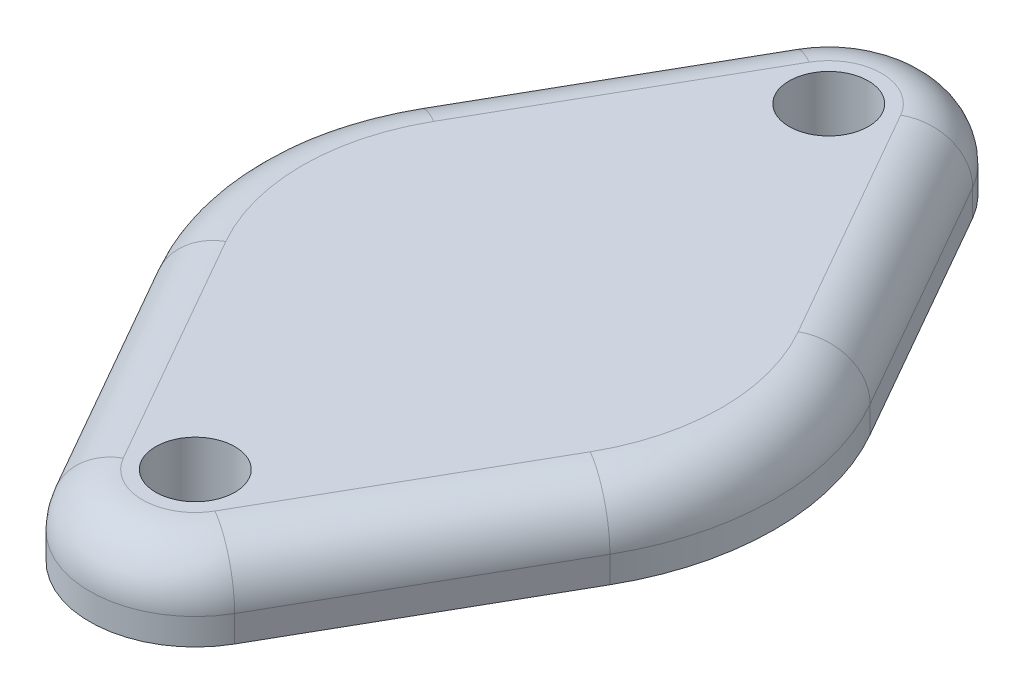
SolidWorks part; units mm, degrees
ref_plane "Спереди" through (0, 0, 0) normal (0, 0, 1) x (1, 0, 0)
ref_plane "Сверху" through (0, 0, 0) normal (0, 1, 0) x (1, 0, 0)
ref_plane "Справа" through (0, 0, 0) normal (1, 0, 0) x (0, 0, -1)
sketch "Эскиз1" plane through (0, 0, 0) normal (0, 1, 0) x (1, 0, 0)
  line L0 (0, 27.0868) -> (0, -27.7364) construction
  line L1 (-11.6506, 0) -> (13.5717, 0) construction
  line L2 (6.8277, 12) -> (-14.7219, 12) construction
  line L3 (6.418, -12) -> (-10.0515, -12) construction
  line L6 (-3.8634, 13.3004) -> (-8.6397, 4.9302)
  line L8 (3.8634, 13.3004) -> (8.6397, 4.9302)
  line L9 (-3.4742, -13.9825) -> (-8.6397, -4.9302)
  line L10 (3.4742, -13.9825) -> (8.6397, -4.9302)
  line L12 (-3.8634, 13.3004) -> (-3.4742, 13.9825)
  line L13 (3.8634, 13.3004) -> (3.4742, 13.9825)
  circle A1 centre (0, 12) radius 1.5
  circle A2 centre (0, -12) radius 1.5
  arc A17 (-8.6397, 4.9302) -> (-8.6397, -4.9302) centre (0, 0) ccw
  arc A20 (3.4742, 13.9825) -> (-3.4742, 13.9825) centre (0, 12) ccw
  arc A21 (8.6397, -4.9302) -> (8.6397, 4.9302) centre (0, 0) ccw
  arc A22 (-3.4742, -13.9825) -> (3.4742, -13.9825) centre (0, -12) ccw
  dimension "D2" = 3
  dimension "D3" = 3
extrude "Бобышка-Вытянуть1" add sketch "Эскиз1" along normal blind 3
fillet "Скругление1" radius 2 8 edges at (0, 3, -16) (6.057, 3, -9.4563) (9.9474, 3, 0) (6.057, 3, 9.4563) (0, 3, 16) (-6.057, 3, 9.4563) (-9.9474, 3, 0) (-6.057, 3, -9.4563)
